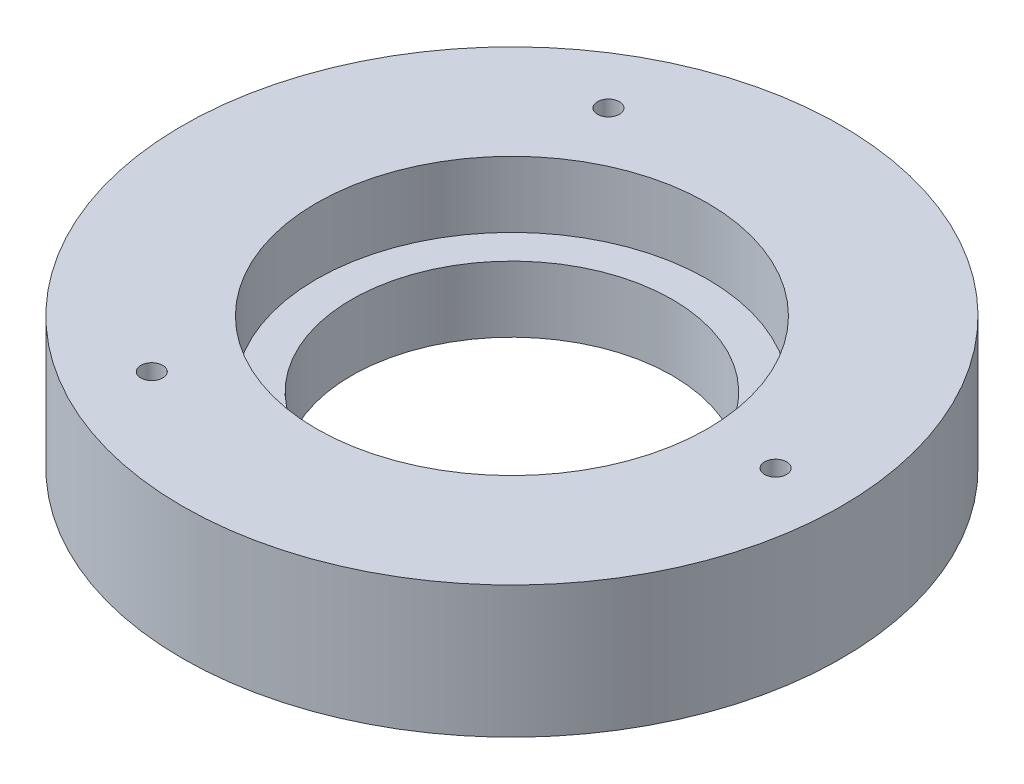
SolidWorks part; units mm, degrees
ref_plane "Front Plane" through (0, 0, 0) normal (0, 0, 1) x (1, 0, 0)
ref_plane "Top Plane" through (0, 0, 0) normal (0, 1, 0) x (1, 0, 0)
ref_plane "Right Plane" through (0, 0, 0) normal (1, 0, 0) x (0, 0, -1)
sketch "Sketch1" plane through (0, 0, 0) normal (0, 1, 0) x (1, 0, 0)
  circle A0 centre (0, 0) radius 95.25
  dimension "D1" = 190.5
extrude "Boss-Extrude1" add sketch "Sketch1" along normal mid plane 38.1
sketch "Sketch2" plane through (0, 19.05, 0) normal (0, 1, 0) x (-1, 0, 0)
  circle A0 centre (0, 0) radius 56.515
  dimension "D1" = 113.03
extrude "Cut-Extrude1" cut sketch "Sketch2" against normal blind 19.05
sketch "Sketch3" plane through (0, -19.05, 0) normal (0, -1, 0) x (1, 0, 0)
  circle A0 centre (0, 0) radius 46.355
  dimension "D1" = 92.71
extrude "Cut-Extrude2" cut sketch "Sketch3" against normal up to surface (19.05 mm away) up to face at (0, 0, 56.515)
sketch "Sketch4" plane through (0, 19.05, 0) normal (0, 1, 0) x (1, 0, 0)
  line L0 (0, 0) -> (118.9659, 0) construction
  line L1 (0, 0) -> (60.9601, -105.586) construction
  circle A0 centre (0, 0) radius 76.2 construction
  circle A1 centre (0, 0) radius 95.25 construction
  dimension "D1" = 19.05
  dimension "D2" = 60
sketch "Sketch7" plane through (0, -19.05, 0) normal (0, -1, 0) x (1, 0, 0)
  line L0 (0, 0) -> (0, -107.0988) construction
  line L1 (0, 0) -> (-106.2319, -61.333) construction
  circle A0 centre (0, 0) radius 89.535 construction
  circle A1 centre (0, 0) radius 95.25 construction
  dimension "D1" = 5.715
  dimension "D2" = 60
sketch "Sketch5" plane through (0, 19.05, 0) normal (0, 1, 0) x (-1, 0, 0)
  line L0 (0, 0) -> (-118.9659, 0) construction
  circle A0 centre (-76.2, 0) radius 3.175
  circle A1 centre (0, 0) radius 76.2 construction
  dimension "D1" = 6.35
extrude "Cut-Extrude3" cut sketch "Sketch5" against normal up to surface (38.1 mm away) up to face at (0, -19.05, -46.355)
pattern_circular "CirPattern1" count 3 over 360 about axis through (0, 0, 0) along (0, 1, 0) of "Cut-Extrude3"
sketch "Sketch6" plane through (0, -19.05, 0) normal (0, -1, 0) x (1, 0, 0)
  line L0 (0, 0) -> (60.9601, 105.586) construction
  circle A0 centre (44.7675, 77.5396) radius 3.175
  circle A2 centre (0, 0) radius 89.535 construction
  point P6 (0, 0)
  point P7 (0, 0)
  dimension "D1" = 6.35
extrude "Cut-Extrude4" cut sketch "Sketch6" against normal blind 19.05
pattern_circular "CirPattern2" count 3 over 360 about axis through (0, 0, 0) along (0, 1, 0) of "Cut-Extrude4"
